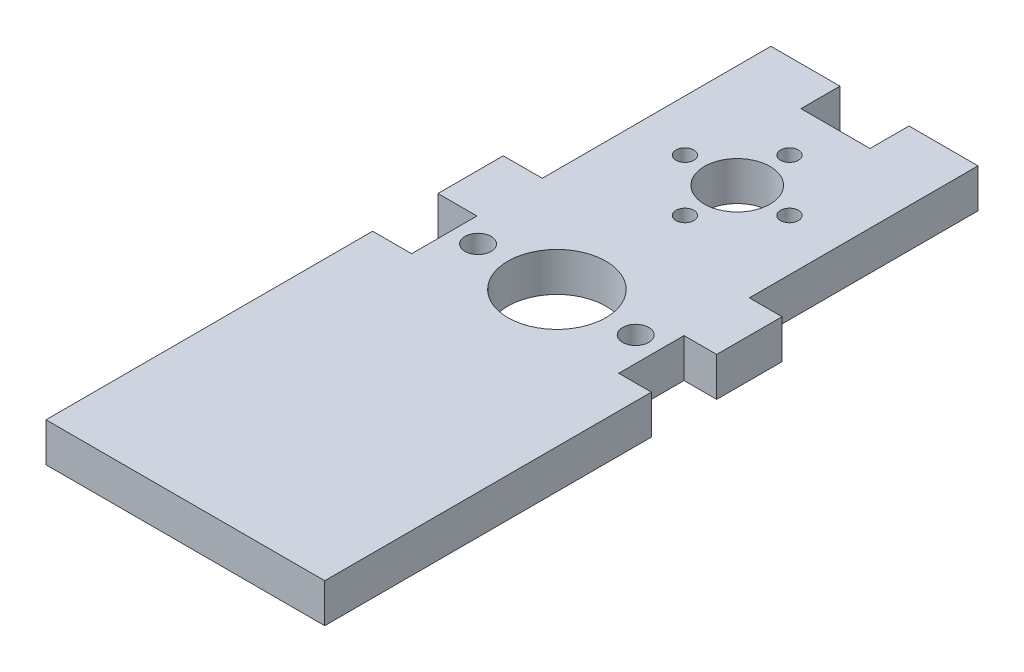
SolidWorks part; units mm, degrees
ref_plane "Front Plane" through (0, 0, 0) normal (0, 0, 1) x (1, 0, 0)
ref_plane "Top Plane" through (0, 0, 0) normal (0, 1, 0) x (1, 0, 0)
ref_plane "Right Plane" through (0, 0, 0) normal (1, 0, 0) x (0, 0, -1)
sketch "Sketch1" plane through (0, 0, 0) normal (0, 1, 0) x (1, 0, 0)
  line L0 (0, 55) -> (31.7, 55) construction
  line L1 (0, 0) -> (31.7, 0)
  line L2 (0, 0) -> (0, 65)
  line L3 (0, 65) -> (10.5667, 65)
  line L4 (31.7, 0) -> (31.7, 65)
  line L5 (15.85, 65) -> (15.85, 0) construction
  line L6 (21.1333, 65) -> (31.7, 65)
  line L8 (21.1333, 65) -> (21.1333, 59.031)
  line L9 (21.1333, 59.031) -> (10.5667, 59.031)
  line L10 (10.5667, 65) -> (10.5667, 59.031)
  line L11 (10.5667, 65) -> (21.1333, 65) construction
  line L12 (15.85, 43.99) -> (10.835, 43.99) construction
  line L13 (15.85, 43.99) -> (20.865, 43.99) construction
  line L14 (15.85, 16.3861) -> (8.35, 16.3861) construction
  line L15 (15.85, 16.3861) -> (23.35, 16.3861) construction
  line L16 (8.35, 16.3861) -> (3.785, 16.3861) construction
  line L17 (23.35, 16.3861) -> (27.915, 16.3861) construction
  circle A0 centre (15.85, 43.99) radius 5.015
  circle A1 centre (15.85, 43.99) radius 11.01 construction
  circle A2 centre (15.85, 16.3861) radius 7.5
  circle A3 centre (3.785, 16.3861) radius 2
  circle A4 centre (27.915, 16.3861) radius 2
  circle A5 centre (7.85, 43.99) radius 1.37
  circle A6 centre (23.85, 43.99) radius 1.37
  circle A7 centre (15.85, 43.99) radius 8 construction
  circle A8 centre (15.85, 51.99) radius 1.37
  circle A9 centre (15.85, 35.99) radius 1.37
  dimension "D4" = 10.03
  dimension "D5" = 22.02
  dimension "D7" = 15
  dimension "D10" = 4
  dimension "D11" = 2.74
  dimension "D13" = 16
  dimension "D1" = 65
  dimension "D2" = 31.7
  dimension "D3" = 10
  dimension "D6" = 27.6039
  dimension "D8" = 5.969
  dimension "D9" = 24.13
extrude "Boss-Extrude1" add sketch "Sketch1" along normal blind 5.969
sketch "Sketch2" plane through (0, 5.969, 0) normal (0, 1, 0) x (1, 0, 0)
  line L5 (0, 65) -> (0, 0) construction
  line L12 (0, 0) -> (-5.969, 0)
  line L17 (0, 0) -> (0, 10)
  line L18 (0, 10) -> (-5.969, 10)
  line L24 (-5.969, 0) -> (-5.969, 10)
  line L26 (0, 20) -> (-5.969, 20)
  line L27 (0, 20) -> (0, 30)
  line L32 (0, 30) -> (-5.969, 30)
  line L35 (-5.969, 20) -> (-5.969, 30)
  line L36 (0, 20) -> (-5.969, 30) construction
  line L37 (0, 30) -> (-5.969, 20) construction
  line L38 (15.85, 0) -> (15.85, 59.031) construction
  line L39 (0, 0) -> (31.7, 0) construction
  line L40 (21.1333, 59.031) -> (10.5667, 59.031) construction
  line L41 (31.7, 30) -> (36.7, 20) construction
  line L42 (31.7, 20) -> (36.7, 30) construction
  line L43 (36.7, 20) -> (36.7, 30)
  line L44 (31.7, 30) -> (36.7, 30)
  line L45 (31.7, 20) -> (31.7, 30)
  line L46 (31.7, 20) -> (36.7, 20)
  line L47 (36.7, 0) -> (36.7, 10)
  line L48 (31.7, 10) -> (36.7, 10)
  line L49 (31.7, 0) -> (31.7, 10)
  line L50 (31.7, 0) -> (36.7, 0)
  point P8 (-2.9845, 25)
  point P25 (34.6845, 25)
  dimension "D1" = 5.969
  dimension "D2" = 10
  dimension "D3" = 10
  dimension "D4" = 5
  dimension "D5" = 5
extrude "Boss-Extrude2" add sketch "Sketch2" against normal blind 5.969
sketch "Sketch3" plane through (0, 5.969, 0) normal (0, 1, 0) x (1, 0, 0)
  line L1 (-5.969, 0) -> (36.7, 0)
  line L2 (-5.969, 0) -> (-5.969, -40)
  line L3 (-5.969, -40) -> (36.7, -40)
  line L4 (36.7, 0) -> (36.7, -40)
  line L5 (-5.969, 0) -> (36.7, -40) construction
  line L6 (-5.969, -40) -> (36.7, 0) construction
  point P4 (15.3655, -20)
  dimension "D1" = 40
extrude "Boss-Extrude3" add sketch "Sketch3" against normal up to surface (5.969 mm away) up to face at (15.85, 0, -34.62)
